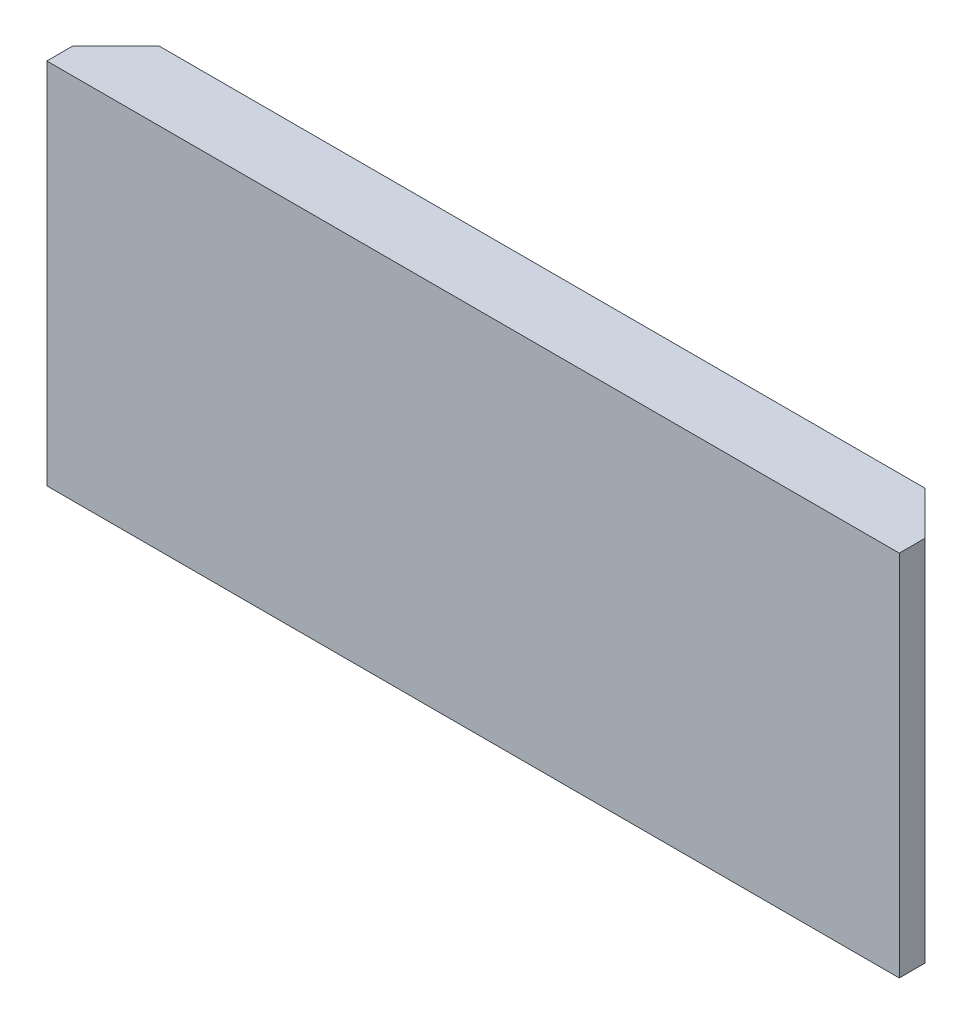
SolidWorks part; units mm, degrees
ref_plane "Front Plane" through (0, 0, 0) normal (0, 0, 1) x (1, 0, 0)
ref_plane "Top Plane" through (0, 0, 0) normal (0, 1, 0) x (1, 0, 0)
ref_plane "Right Plane" through (0, 0, 0) normal (1, 0, 0) x (0, 0, -1)
sketch "Sketch1" plane through (0, 0, 0) normal (0, 0, 1) x (1, 0, 0)
  line L1 (-78.35, 47.1944) -> (119.05, 47.1944)
  line L2 (-78.35, 47.1944) -> (-78.35, -38.015)
  line L3 (-78.35, -38.015) -> (119.05, -38.015)
  line L4 (119.05, 47.1944) -> (119.05, -38.015)
extrude "Boss-Extrude1" add sketch "Sketch1" along normal blind 6
sketch "Sketch2" plane through (0, 47.1944, 0) normal (0, 1, 0) x (1, 0, 0)
  line L0 (-78.35, 0) -> (-68.35, 10)
  line L1 (-68.35, 10) -> (109.05, 10)
  line L2 (119.05, 0) -> (-78.35, 0) construction
  line L3 (119.05, 0) -> (109.05, 10)
  line L8 (119.05, 0) -> (-78.35, 0)
  line L9 (-78.35, 0) -> (-78.35, -6)
  line L10 (-78.35, -6) -> (119.05, -6)
  line L11 (119.05, -6) -> (119.05, 0)
  line L13 (-78.35, 0) -> (-78.35, -6)
  line L14 (-78.35, -6) -> (119.05, -6)
  line L15 (119.05, -6) -> (119.05, 0)
  dimension "D1" = 10
  dimension "D2" = 0
extrude "Boss-Extrude2" add sketch "Sketch2" against normal blind 10
